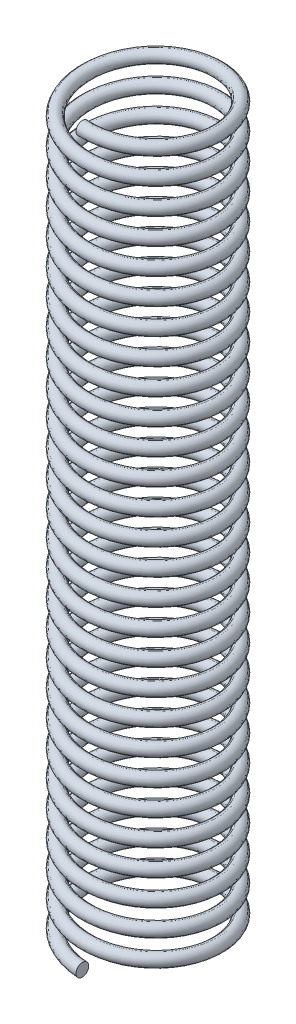
SolidWorks part; units mm, degrees
ref_plane "Front Plane" through (0, 0, 0) normal (0, 0, 1) x (1, 0, 0)
ref_plane "Top Plane" through (0, 0, 0) normal (0, 1, 0) x (1, 0, 0)
ref_plane "Right Plane" through (0, 0, 0) normal (1, 0, 0) x (0, 0, -1)
sketch "Sketch1" plane through (0, 0, 0) normal (0, 1, 0) x (1, 0, 0)
  circle A0 centre (0, 0) radius 9
  dimension "D1" = 18
curve "Helix/Spiral2" pitch 3.5714 height 100 turns 28
sketch "Sketch2" plane through (0, 0, 0) normal (1, 0, 0) x (0, 0, -1)
  circle A0 centre (-9, 0) radius 0.875
  spline S0 degree 3 poles (-9, 0) (-9, 0.0739) (-8.5314, 0.2234) (-6.5296, 0.4464) (-3.5338, 0.6697) (0, 0.8929) (3.5338, 1.1161) (6.5296, 1.3393) (8.5314, 1.5625) (9.2343, 1.7857) (8.5314, 2.0089) (6.5296, 2.2321) (3.5338, 2.4554) (0, 2.6786) (-3.5338, 2.9018) (-6.5296, 3.125) (-8.5314, 3.3482) (-9.2343, 3.5714) (-8.5314, 3.7946) (-6.5296, 4.0179) (-3.5338, 4.2411) (0, 4.4643) (3.5338, 4.6875) (6.5296, 4.9107) (8.5314, 5.1339) (9.2343, 5.3571) (8.5314, 5.5804) (6.5296, 5.8036) (3.5338, 6.0268) (0, 6.25) (-3.5338, 6.4732) (-6.5296, 6.6964) (-8.5314, 6.9196) (-9.2343, 7.1429) (-8.5314, 7.3661) (-6.5296, 7.5893) (-3.5338, 7.8125) (0, 8.0357) (3.5338, 8.2589) (6.5296, 8.4821) (8.5314, 8.7054) (9.2343, 8.9286) (8.5314, 9.1518) (6.5296, 9.375) (3.5338, 9.5982) (0, 9.8214) (-3.5338, 10.0446) (-6.5296, 10.2679) (-8.5314, 10.4911) (-9.2343, 10.7143) (-8.5314, 10.9375) (-6.5296, 11.1607) (-3.5338, 11.3839) (0, 11.6071) (3.5338, 11.8304) (6.5296, 12.0536) (8.5314, 12.2768) (9.2343, 12.5) (8.5314, 12.7232) (6.5296, 12.9464) (3.5338, 13.1696) (0, 13.3929) (-3.5338, 13.6161) (-6.5296, 13.8393) (-8.5314, 14.0625) (-9.2343, 14.2857) (-8.5314, 14.5089) (-6.5296, 14.7321) (-3.5338, 14.9554) (0, 15.1786) (3.5338, 15.4018) (6.5296, 15.625) (8.5314, 15.8482) (9.2343, 16.0714) (8.5314, 16.2946) (6.5296, 16.5179) (3.5338, 16.7411) (0, 16.9643) (-3.5338, 17.1875) (-6.5296, 17.4107) (-8.5314, 17.6339) (-9.2343, 17.8571) (-8.5314, 18.0804) (-6.5296, 18.3036) (-3.5338, 18.5268) (0, 18.75) (3.5338, 18.9732) (6.5296, 19.1964) (8.5314, 19.4196) (9.2343, 19.6429) (8.5314, 19.8661) (6.5296, 20.0893) (3.5338, 20.3125) (0, 20.5357) (-3.5338, 20.7589) (-6.5296, 20.9821) (-8.5314, 21.2054) (-9.2343, 21.4286) (-8.5314, 21.6518) (-6.5296, 21.875) (-3.5338, 22.0982) (0, 22.3214) (3.5338, 22.5446) (6.5296, 22.7679) (8.5314, 22.9911) (9.2343, 23.2143) (8.5314, 23.4375) (6.5296, 23.6607) (3.5338, 23.8839) (0, 24.1071) (-3.5338, 24.3304) (-6.5296, 24.5536) (-8.5314, 24.7768) (-9.2343, 25) (-8.5314, 25.2232) (-6.5296, 25.4464) (-3.5338, 25.6696) (0, 25.8929) (3.5338, 26.1161) (6.5296, 26.3393) (8.5314, 26.5625) (9.2343, 26.7857) (8.5314, 27.0089) (6.5296, 27.2321) (3.5338, 27.4554) (0, 27.6786) (-3.5338, 27.9018) (-6.5296, 28.125) (-8.5314, 28.3482) (-9.2343, 28.5714) (-8.5314, 28.7946) (-6.5296, 29.0179) (-3.5338, 29.2411) (0, 29.4643) (3.5338, 29.6875) (6.5296, 29.9107) (8.5314, 30.1339) (9.2343, 30.3571) (8.5314, 30.5804) (6.5296, 30.8036) (3.5338, 31.0268) (0, 31.25) (-3.5338, 31.4732) (-6.5296, 31.6964) (-8.5314, 31.9196) (-9.2343, 32.1429) (-8.5314, 32.3661) (-6.5296, 32.5893) (-3.5338, 32.8125) (0, 33.0357) (3.5338, 33.2589) (6.5296, 33.4821) (8.5314, 33.7054) (9.2343, 33.9286) (8.5314, 34.1518) (6.5296, 34.375) (3.5338, 34.5982) (0, 34.8214) (-3.5338, 35.0446) (-6.5296, 35.2679) (-8.5314, 35.4911) (-9.2343, 35.7143) (-8.5314, 35.9375) (-6.5296, 36.1607) (-3.5338, 36.3839) (0, 36.6071) (3.5338, 36.8304) (6.5296, 37.0536) (8.5314, 37.2768) (9.2343, 37.5) (8.5314, 37.7232) (6.5296, 37.9464) (3.5338, 38.1696) (0, 38.3929) (-3.5338, 38.6161) (-6.5296, 38.8393) (-8.5314, 39.0625) (-9.2343, 39.2857) (-8.5314, 39.5089) (-6.5296, 39.7321) (-3.5338, 39.9554) (0, 40.1786) (3.5338, 40.4018) (6.5296, 40.625) (8.5314, 40.8482) (9.2343, 41.0714) (8.5314, 41.2946) (6.5296, 41.5179) (3.5338, 41.7411) (0, 41.9643) (-3.5338, 42.1875) (-6.5296, 42.4107) (-8.5314, 42.6339) (-9.2343, 42.8571) (-8.5314, 43.0804) (-6.5296, 43.3036) (-3.5338, 43.5268) (0, 43.75) (3.5338, 43.9732) (6.5296, 44.1964) (8.5314, 44.4196) (9.2343, 44.6429) (8.5314, 44.8661) (6.5296, 45.0893) (3.5338, 45.3125) (0, 45.5357) (-3.5338, 45.7589) (-6.5296, 45.9821) (-8.5314, 46.2054) (-9.2343, 46.4286) (-8.5314, 46.6518) (-6.5296, 46.875) (-3.5338, 47.0982) (0, 47.3214) (3.5338, 47.5446) (6.5296, 47.7679) (8.5314, 47.9911) (9.2343, 48.2143) (8.5314, 48.4375) (6.5296, 48.6607) (3.5338, 48.8839) (0, 49.1071) (-3.5338, 49.3304) (-6.5296, 49.5536) (-8.5314, 49.7768) (-9.2343, 50) (-8.5314, 50.2232) (-6.5296, 50.4464) (-3.5338, 50.6696) (0, 50.8929) (3.5338, 51.1161) (6.5296, 51.3393) (8.5314, 51.5625) (9.2343, 51.7857) (8.5314, 52.0089) (6.5296, 52.2321) (3.5338, 52.4554) (0, 52.6786) (-3.5338, 52.9018) (-6.5296, 53.125) (-8.5314, 53.3482) (-9.2343, 53.5714) (-8.5314, 53.7946) (-6.5296, 54.0179) (-3.5338, 54.2411) (0, 54.4643) (3.5338, 54.6875) (6.5296, 54.9107) (8.5314, 55.1339) (9.2343, 55.3571) (8.5314, 55.5804) (6.5296, 55.8036) (3.5338, 56.0268) (0, 56.25) (-3.5338, 56.4732) (-6.5296, 56.6964) (-8.5314, 56.9196) (-9.2343, 57.1429) (-8.5314, 57.3661) (-6.5296, 57.5893) (-3.5338, 57.8125) (0, 58.0357) (3.5338, 58.2589) (6.5296, 58.4821) (8.5314, 58.7054) (9.2343, 58.9286) (8.5314, 59.1518) (6.5296, 59.375) (3.5338, 59.5982) (0, 59.8214) (-3.5338, 60.0446) (-6.5296, 60.2679) (-8.5314, 60.4911) (-9.2343, 60.7143) (-8.5314, 60.9375) (-6.5296, 61.1607) (-3.5338, 61.3839) (0, 61.6071) (3.5338, 61.8304) (6.5296, 62.0536) (8.5314, 62.2768) (9.2343, 62.5) (8.5314, 62.7232) (6.5296, 62.9464) (3.5338, 63.1696) (0, 63.3929) (-3.5338, 63.6161) (-6.5296, 63.8393) (-8.5314, 64.0625) (-9.2343, 64.2857) (-8.5314, 64.5089) (-6.5296, 64.7321) (-3.5338, 64.9554) (0, 65.1786) (3.5338, 65.4018) (6.5296, 65.625) (8.5314, 65.8482) (9.2343, 66.0714) (8.5314, 66.2946) (6.5296, 66.5179) (3.5338, 66.7411) (0, 66.9643) (-3.5338, 67.1875) (-6.5296, 67.4107) (-8.5314, 67.6339) (-9.2343, 67.8571) (-8.5314, 68.0804) (-6.5296, 68.3036) (-3.5338, 68.5268) (0, 68.75) (3.5338, 68.9732) (6.5296, 69.1964) (8.5314, 69.4196) (9.2343, 69.6429) (8.5314, 69.8661) (6.5296, 70.0893) (3.5338, 70.3125) (0, 70.5357) (-3.5338, 70.7589) (-6.5296, 70.9821) (-8.5314, 71.2054) (-9.2343, 71.4286) (-8.5314, 71.6518) (-6.5296, 71.875) (-3.5338, 72.0982) (0, 72.3214) (3.5338, 72.5446) (6.5296, 72.7679) (8.5314, 72.9911) (9.2343, 73.2143) (8.5314, 73.4375) (6.5296, 73.6607) (3.5338, 73.8839) (0, 74.1071) (-3.5338, 74.3304) (-6.5296, 74.5536) (-8.5314, 74.7768) (-9.2343, 75) (-8.5314, 75.2232) (-6.5296, 75.4464) (-3.5338, 75.6696) (0, 75.8929) (3.5338, 76.1161) (6.5296, 76.3393) (8.5314, 76.5625) (9.2343, 76.7857) (8.5314, 77.0089) (6.5296, 77.2321) (3.5338, 77.4554) (0, 77.6786) (-3.5338, 77.9018) (-6.5296, 78.125) (-8.5314, 78.3482) (-9.2343, 78.5714) (-8.5314, 78.7946) (-6.5296, 79.0179) (-3.5338, 79.2411) (0, 79.4643) (3.5338, 79.6875) (6.5296, 79.9107) (8.5314, 80.1339) (9.2343, 80.3571) (8.5314, 80.5804) (6.5296, 80.8036) (3.5338, 81.0268) (0, 81.25) (-3.5338, 81.4732) (-6.5296, 81.6964) (-8.5314, 81.9196) (-9.2343, 82.1429) (-8.5314, 82.3661) (-6.5296, 82.5893) (-3.5338, 82.8125) (0, 83.0357) (3.5338, 83.2589) (6.5296, 83.4821) (8.5314, 83.7054) (9.2343, 83.9286) (8.5314, 84.1518) (6.5296, 84.375) (3.5338, 84.5982) (0, 84.8214) (-3.5338, 85.0446) (-6.5296, 85.2679) (-8.5314, 85.4911) (-9.2343, 85.7143) (-8.5314, 85.9375) (-6.5296, 86.1607) (-3.5338, 86.3839) (0, 86.6071) (3.5338, 86.8304) (6.5296, 87.0536) (8.5314, 87.2768) (9.2343, 87.5) (8.5314, 87.7232) (6.5296, 87.9464) (3.5338, 88.1696) (0, 88.3929) (-3.5338, 88.6161) (-6.5296, 88.8393) (-8.5314, 89.0625) (-9.2343, 89.2857) (-8.5314, 89.5089) (-6.5296, 89.7321) (-3.5338, 89.9554) (0, 90.1786) (3.5338, 90.4018) (6.5296, 90.625) (8.5314, 90.8482) (9.2343, 91.0714) (8.5314, 91.2946) (6.5296, 91.5179) (3.5338, 91.7411) (0, 91.9643) (-3.5338, 92.1875) (-6.5296, 92.4107) (-8.5314, 92.6339) (-9.2343, 92.8571) (-8.5314, 93.0804) (-6.5296, 93.3036) (-3.5338, 93.5268) (0, 93.75) (3.5338, 93.9732) (6.5296, 94.1964) (8.5314, 94.4196) (9.2343, 94.6429) (8.5314, 94.8661) (6.5296, 95.0893) (3.5338, 95.3125) (0, 95.5357) (-3.5338, 95.7589) (-6.5296, 95.9821) (-8.5314, 96.2054) (-9.2343, 96.4286) (-8.5314, 96.6518) (-6.5296, 96.875) (-3.5338, 97.0982) (0, 97.3214) (3.5338, 97.5446) (6.5296, 97.7679) (8.5314, 97.9911) (9.2343, 98.2143) (8.5314, 98.4375) (6.5296, 98.6607) (3.5338, 98.8839) (0, 99.1071) (-3.5338, 99.3303) (-6.5296, 99.5536) (-8.5314, 99.7766) (-9, 99.9261) (-9, 100) knots 0 0 0 0 0.002232 0.004464 0.006696 0.008929 0.011161 0.013393 0.015625 0.017857 0.020089 0.022321 0.024554 0.026786 0.029018 0.03125 0.033482 0.035714 0.037946 0.040179 0.042411 0.044643 0.046875 0.049107 0.051339 0.053571 0.055804 0.058036 0.060268 0.0625 0.064732 0.066964 0.069196 0.071429 0.073661 0.075893 0.078125 0.080357 0.082589 0.084821 0.087054 0.089286 0.091518 0.09375 0.095982 0.098214 0.100446 0.102679 0.104911 0.107143 0.109375 0.111607 0.113839 0.116071 0.118304 0.120536 0.122768 0.125 0.127232 0.129464 0.131696 0.133929 0.136161 0.138393 0.140625 0.142857 0.145089 0.147321 0.149554 0.151786 0.154018 0.15625 0.158482 0.160714 0.162946 0.165179 0.167411 0.169643 0.171875 0.174107 0.176339 0.178571 0.180804 0.183036 0.185268 0.1875 0.189732 0.191964 0.194196 0.196429 0.198661 0.200893 0.203125 0.205357 0.207589 0.209821 0.212054 0.214286 0.216518 0.21875 0.220982 0.223214 0.225446 0.227679 0.229911 0.232143 0.234375 0.236607 0.238839 0.241071 0.243304 0.245536 0.247768 0.25 0.252232 0.254464 0.256696 0.258929 0.261161 0.263393 0.265625 0.267857 0.270089 0.272321 0.274554 0.276786 0.279018 0.28125 0.283482 0.285714 0.287946 0.290179 0.292411 0.294643 0.296875 0.299107 0.301339 0.303571 0.305804 0.308036 0.310268 0.3125 0.314732 0.316964 0.319196 0.321429 0.323661 0.325893 0.328125 0.330357 0.332589 0.334821 0.337054 0.339286 0.341518 0.34375 0.345982 0.348214 0.350446 0.352679 0.354911 0.357143 0.359375 0.361607 0.363839 0.366071 0.368304 0.370536 0.372768 0.375 0.377232 0.379464 0.381696 0.383929 0.386161 0.388393 0.390625 0.392857 0.395089 0.397321 0.399554 0.401786 0.404018 0.40625 0.408482 0.410714 0.412946 0.415179 0.417411 0.419643 0.421875 0.424107 0.426339 0.428571 0.430804 0.433036 0.435268 0.4375 0.439732 0.441964 0.444196 0.446429 0.448661 0.450893 0.453125 0.455357 0.457589 0.459821 0.462054 0.464286 0.466518 0.46875 0.470982 0.473214 0.475446 0.477679 0.479911 0.482143 0.484375 0.486607 0.488839 0.491071 0.493304 0.495536 0.497768 0.5 0.502232 0.504464 0.506696 0.508929 0.511161 0.513393 0.515625 0.517857 0.520089 0.522321 0.524554 0.526786 0.529018 0.53125 0.533482 0.535714 0.537946 0.540179 0.542411 0.544643 0.546875 0.549107 0.551339 0.553571 0.555804 0.558036 0.560268 0.5625 0.564732 0.566964 0.569196 0.571429 0.573661 0.575893 0.578125 0.580357 0.582589 0.584821 0.587054 0.589286 0.591518 0.59375 0.595982 0.598214 0.600446 0.602679 0.604911 0.607143 0.609375 0.611607 0.613839 0.616071 0.618304 0.620536 0.622768 0.625 0.627232 0.629464 0.631696 0.633929 0.636161 0.638393 0.640625 0.642857 0.645089 0.647321 0.649554 0.651786 0.654018 0.65625 0.658482 0.660714 0.662946 0.665179 0.667411 0.669643 0.671875 0.674107 0.676339 0.678571 0.680804 0.683036 0.685268 0.6875 0.689732 0.691964 0.694196 0.696429 0.698661 0.700893 0.703125 0.705357 0.707589 0.709821 0.712054 0.714286 0.716518 0.71875 0.720982 0.723214 0.725446 0.727679 0.729911 0.732143 0.734375 0.736607 0.738839 0.741071 0.743304 0.745536 0.747768 0.75 0.752232 0.754464 0.756696 0.758929 0.761161 0.763393 0.765625 0.767857 0.770089 0.772321 0.774554 0.776786 0.779018 0.78125 0.783482 0.785714 0.787946 0.790179 0.792411 0.794643 0.796875 0.799107 0.801339 0.803571 0.805804 0.808036 0.810268 0.8125 0.814732 0.816964 0.819196 0.821429 0.823661 0.825893 0.828125 0.830357 0.832589 0.834821 0.837054 0.839286 0.841518 0.84375 0.845982 0.848214 0.850446 0.852679 0.854911 0.857143 0.859375 0.861607 0.863839 0.866071 0.868304 0.870536 0.872768 0.875 0.877232 0.879464 0.881696 0.883929 0.886161 0.888393 0.890625 0.892857 0.895089 0.897321 0.899554 0.901786 0.904018 0.90625 0.908482 0.910714 0.912946 0.915179 0.917411 0.919643 0.921875 0.924107 0.926339 0.928571 0.930804 0.933036 0.935268 0.9375 0.939732 0.941964 0.944196 0.946429 0.948661 0.950893 0.953125 0.955357 0.957589 0.959821 0.962054 0.964286 0.966518 0.96875 0.970982 0.973214 0.975446 0.977679 0.979911 0.982143 0.984375 0.986607 0.988839 0.991071 0.993304 0.995536 0.997768 1 1 1 1 construction
  dimension "D1" = 1.75
sweep "Sweep1" add profiles "Sketch2" path "Helix/Spiral2"
